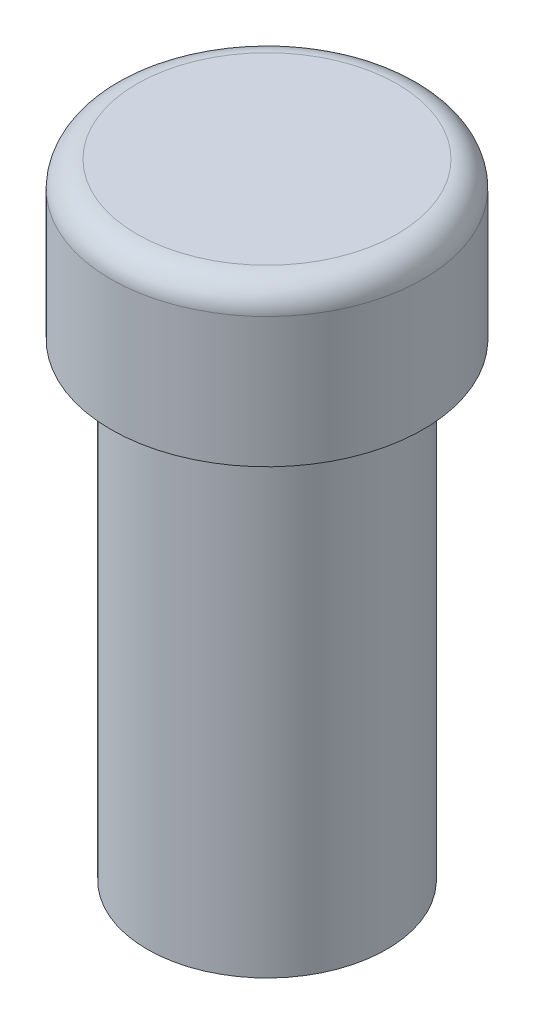
SolidWorks part; units mm, degrees
ref_plane "Front Plane" through (0, 0, 0) normal (0, 0, 1) x (1, 0, 0)
ref_plane "Top Plane" through (0, 0, 0) normal (0, 1, 0) x (1, 0, 0)
ref_plane "Right Plane" through (0, 0, 0) normal (1, 0, 0) x (0, 0, -1)
sketch "Sketch1" plane through (0, 0, 0) normal (0, 1, 0) x (1, 0, 0)
  circle A0 centre (0, 0) radius 3
  dimension "D1" = 6
extrude "Boss-Extrude1" add sketch "Sketch1" along normal blind 3
fillet "Fillet1" radius 0.5 1 edges at (0, 3, 3)
sketch "Sketch2" plane through (0, 0, 0) normal (0, -1, 0) x (1, 0, 0)
  circle A0 centre (0, 0) radius 2.3
  dimension "D1" = 4.6
extrude "Boss-Extrude2" add sketch "Sketch2" along normal blind 9
